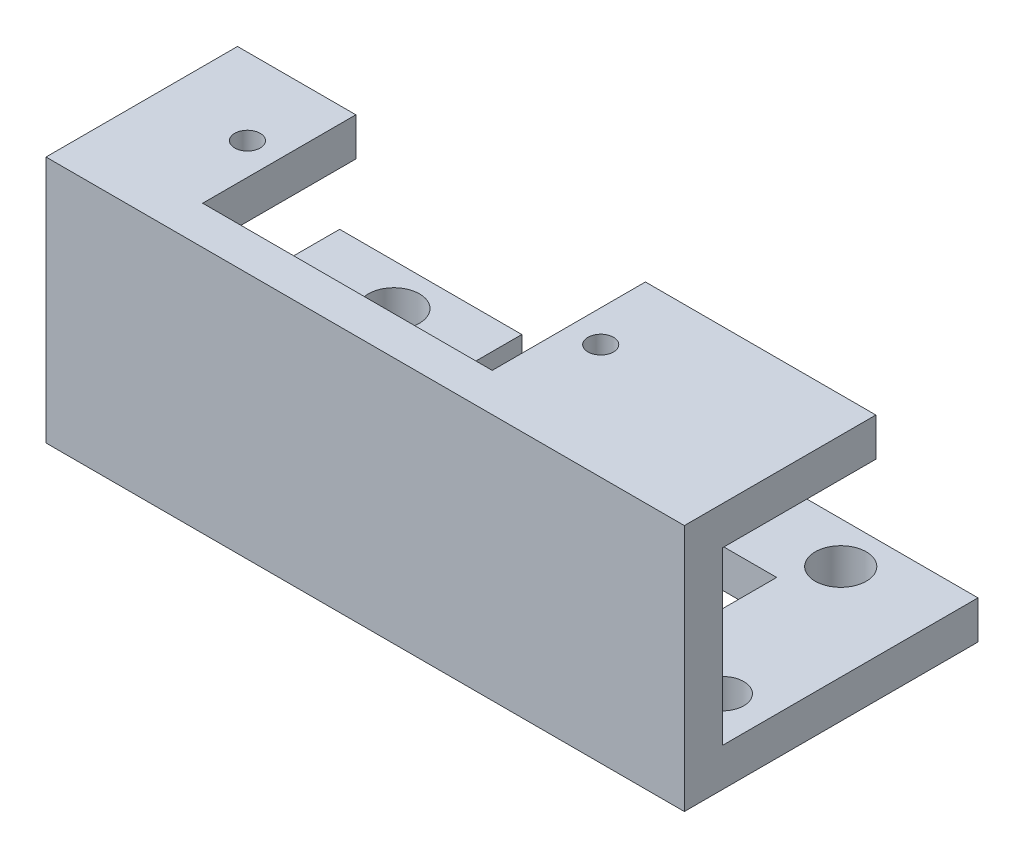
SolidWorks part; units mm, degrees
ref_plane "前视基准面" through (0, 0, 0) normal (0, 0, 1) x (1, 0, 0)
ref_plane "上视基准面" through (0, 0, 0) normal (0, 1, 0) x (1, 0, 0)
ref_plane "右视基准面" through (0, 0, 0) normal (1, 0, 0) x (0, 0, -1)
sketch "草图1" plane through (0, 0, 0) normal (0, 0, 1) x (1, 0, 0)
  line L1 (0, 0) -> (50, 0)
  line L2 (0, 0) -> (0, 19.4)
  line L3 (0, 19.4) -> (50, 19.4)
  line L4 (50, 0) -> (50, 19.4)
extrude "凸台-拉伸1" add sketch "草图1" along normal blind 3
sketch "草图2" plane through (0, 0, 0) normal (0, 0, -1) x (-1, 0, 0)
  line L0 (-50, 19.4) -> (0, 19.4) construction
  line L5 (-25, 19.4) -> (-25, 0)
  line L6 (0, 0) -> (-50, 0) construction
  line L8 (-50, 19.4) -> (-31.95, 19.4)
  line L9 (-50, 19.4) -> (-50, 16.4)
  line L10 (-50, 16.4) -> (-31.95, 16.4)
  line L11 (-31.95, 19.4) -> (-31.95, 16.4)
  line L12 (0, 19.4) -> (-9.27, 19.4)
  line L13 (0, 19.4) -> (0, 16.4)
  line L14 (0, 16.4) -> (-9.27, 16.4)
  line L15 (-9.27, 19.4) -> (-9.27, 16.4)
extrude "凸台-拉伸3" add sketch "草图2" along normal blind 12 contours L9 L8 L11 L10 | L13 L12 L15 L14
sketch "草图5" plane through (0, 19.4, 0) normal (0, 1, 0) x (1, 0, 0)
  line L0 (50, -3) -> (0, -3) construction
  line L1 (25, -3) -> (25, 0)
  line L2 (31.95, 0) -> (9.27, 0) construction
  line L3 (25, 0) -> (34.45, 0)
  line L4 (34.45, 0) -> (34.45, 6)
  line L5 (25, 0) -> (6.78, 0)
  line L6 (6.78, 0) -> (6.78, 6)
  circle A0 centre (34.45, 6) radius 1
  circle A1 centre (6.78, 6) radius 1
extrude "切除-拉伸1" cut sketch "草图5" against normal blind 4
sketch "草图6" plane through (0, 0, 0) normal (0, 0, -1) x (-1, 0, 0)
  line L0 (0, 0) -> (-50, 0) construction
  line L1 (-25, 0) -> (-25, 19.4)
  line L2 (-31.95, 19.4) -> (-9.27, 19.4) construction
  line L3 (-50, 2.9967) -> (-40.73, 2.9967)
  line L4 (0, 0) -> (-9.27, 0)
  line L5 (0, 0) -> (0, 2.9967)
  line L6 (0, 2.9967) -> (-9.27, 2.9967)
  line L7 (-9.27, 0) -> (-9.27, 2.9967)
  line L8 (-40.73, 0) -> (-40.73, 2.9967)
  line L9 (-50, 0) -> (-40.73, 0)
  line L10 (-50, 0) -> (-50, 2.9967)
  line M10 (-50, 16.4) -> (-50, 0)
  line M11 (-50, 0) -> (0, 0)
extrude "凸台-拉伸5" add sketch "草图6" along normal blind 20 contours L8 L3 M11 M10 | L6 L7 L4 L5
sketch "草图9" plane through (9.27, 0, 0) normal (1, 0, 0) x (0, 0, -1)
  line L0 (20, 0) -> (0, 0) construction
  line L1 (20, 2.9967) -> (13.5, 2.9967)
  line L2 (20, 2.9967) -> (20, 0)
  line L3 (20, 0) -> (13.5, 0)
  line L4 (13.5, 2.9967) -> (13.5, 0)
extrude "凸台-拉伸6" add sketch "草图9" along normal blind 5
sketch "草图10" plane through (40.73, 0, 0) normal (-1, 0, 0) x (0, 0, 1)
  line L0 (-20, 0) -> (0, 0) construction
  line L1 (-20, 2.9967) -> (-13.5, 2.9967)
  line L2 (-20, 2.9967) -> (-20, 0)
  line L3 (-20, 0) -> (-13.5, 0)
  line L4 (-13.5, 2.9967) -> (-13.5, 0)
extrude "凸台-拉伸7" add sketch "草图10" along normal blind 5
sketch "草图11" plane through (0, 2.9967, 0) normal (0, 1, 0) x (1, 0, 0)
  line L0 (35.73, 13.5) -> (35.73, 20) construction
  line L1 (50, 0) -> (46.5, 0)
  line L2 (50, 0) -> (40.73, 0) construction
  line L3 (35.73, 16.75) -> (42.5, 16.75)
  line L4 (46.5, 0) -> (46.5, 3.5)
  circle A0 centre (42.5, 16.75) radius 2
  circle A1 centre (46.5, 3.5) radius 1.65
extrude "切除-拉伸3" cut sketch "草图11" against normal blind 5
sketch "草图12" plane through (0, 2.9967, 0) normal (0, 1, 0) x (1, 0, 0)
  line L0 (14.27, 20) -> (14.27, 13.5) construction
  line L1 (14.27, 16.75) -> (7.5, 16.75)
  line L2 (0, 0) -> (3.5, 0)
  line L3 (0, 0) -> (9.27, 0) construction
  line L4 (3.5, 0) -> (3.5, 3.5)
  circle A0 centre (7.5, 16.75) radius 2
  circle A1 centre (3.5, 3.5) radius 1.65
extrude "切除-拉伸4" cut sketch "草图12" against normal blind 5
